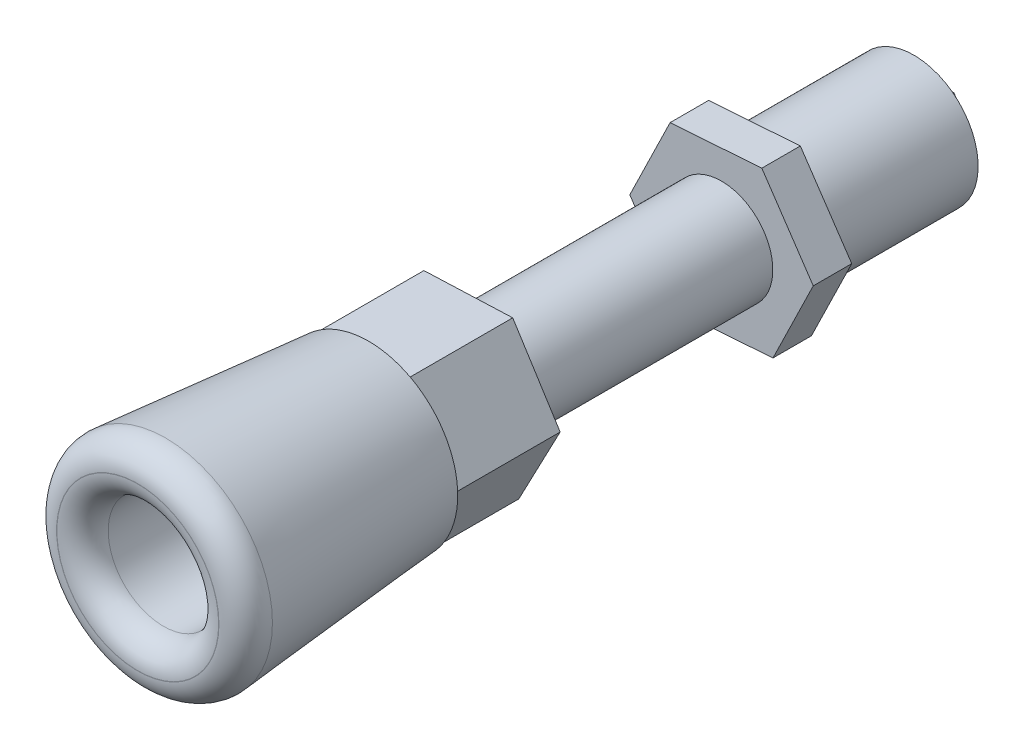
SolidWorks part; units mm, degrees
ref_plane "前视基准面" through (0, 0, 0) normal (0, 0, 1) x (1, 0, 0)
ref_plane "上视基准面" through (0, 0, 0) normal (0, 1, 0) x (1, 0, 0)
ref_plane "右视基准面" through (0, 0, 0) normal (1, 0, 0) x (0, 0, -1)
sketch "草图1" plane through (0, 0, 0) normal (0, 0, 1) x (1, 0, 0)
  line L1 (-3.698, 5.8587) -> (-6.9228, -0.2733)
  line L2 (-6.9228, -0.2733) -> (-3.2248, -6.132)
  line L3 (-3.2248, -6.132) -> (3.698, -5.8587)
  line L4 (3.698, -5.8587) -> (6.9228, 0.2733)
  line L5 (6.9228, 0.2733) -> (3.2248, 6.132)
  line L6 (3.2248, 6.132) -> (-3.698, 5.8587)
  circle A0 centre (0, 0) radius 6 construction
  dimension "D1" = 12
extrude "凸台-拉伸1" add sketch "草图1" along normal blind 8
sketch "草图2" plane through (0, 0, 0) normal (0, 0, -1) x (-1, 0, 0)
  circle A0 centre (0, 0) radius 4
  dimension "D1" = 8
extrude "凸台-拉伸2" add sketch "草图2" along normal blind 19.5
sketch "草图3" plane through (0, 0, -19.5) normal (0, 0, -1) x (-1, 0, 0)
  line L1 (4.0077, 5.9413) -> (-3.1415, 6.4414)
  line L2 (-3.1415, 6.4414) -> (-7.1492, 0.5001)
  line L3 (-7.1492, 0.5001) -> (-4.0077, -5.9413)
  line L4 (-4.0077, -5.9413) -> (3.1415, -6.4414)
  line L5 (3.1415, -6.4414) -> (7.1492, -0.5001)
  line L6 (7.1492, -0.5001) -> (4.0077, 5.9413)
  circle A0 centre (0, 0) radius 6.2065 construction
extrude "凸台-拉伸3" add sketch "草图3" along normal blind 3
sketch "草图4" plane through (0, 0, -22.5) normal (0, 0, -1) x (-1, 0, 0)
  circle A0 centre (0, 0) radius 5
  dimension "10" = 10
extrude "凸台-拉伸4" add sketch "草图4" along normal blind 12
sketch "草图5" plane through (0, 0, -34.5) normal (0, 0, -1) x (-1, 0, 0)
  line L1 (1.1871, 1.981) -> (-1.122, 2.0185)
  line L2 (-1.122, 2.0185) -> (-2.3091, 0.0375)
  line L3 (-2.3091, 0.0375) -> (-1.1871, -1.981)
  line L4 (-1.1871, -1.981) -> (1.122, -2.0185)
  line L5 (1.122, -2.0185) -> (2.3091, -0.0375)
  line L6 (2.3091, -0.0375) -> (1.1871, 1.981)
  circle A0 centre (0, 0) radius 2 construction
  dimension "D1" = 4
extrude "凸台-拉伸5" add sketch "草图5" along normal blind 2
sketch "草图10" plane through (0, 0, 8) normal (0, 0, 1) x (1, 0, 0)
  circle A0 centre (0, 0) radius 6.9371
extrude "凸台-拉伸6" add sketch "草图10" along normal blind 18 draft 5 draft outward yes
sketch "草图11" plane through (0, 0, 26) normal (0, 0, 1) x (1, 0, 0)
  circle A0 centre (0, 0) radius 4.3038
extrude "切除-拉伸2" cut sketch "草图11" against normal blind 18
sketch "草图12" plane through (0, 0, 8) normal (0, 0, 1) x (1, 0, 0)
  circle A0 centre (0, 0) radius 1.7312
extrude "切除-拉伸3" cut sketch "草图12" against normal up to surface (8 mm away) up to face at (-4, 0, 0)
fillet "圆角1" radius 2 2 edges at (8.5119, 0, 26) (4.3038, 0, 26)
sketch "草图13" plane through (0, 0, -36.5) normal (0, 0, -1) x (-1, 0, 0)
  circle A0 centre (0, 0) radius 0.9237
extrude "切除-拉伸4" cut sketch "草图13" against normal through all
